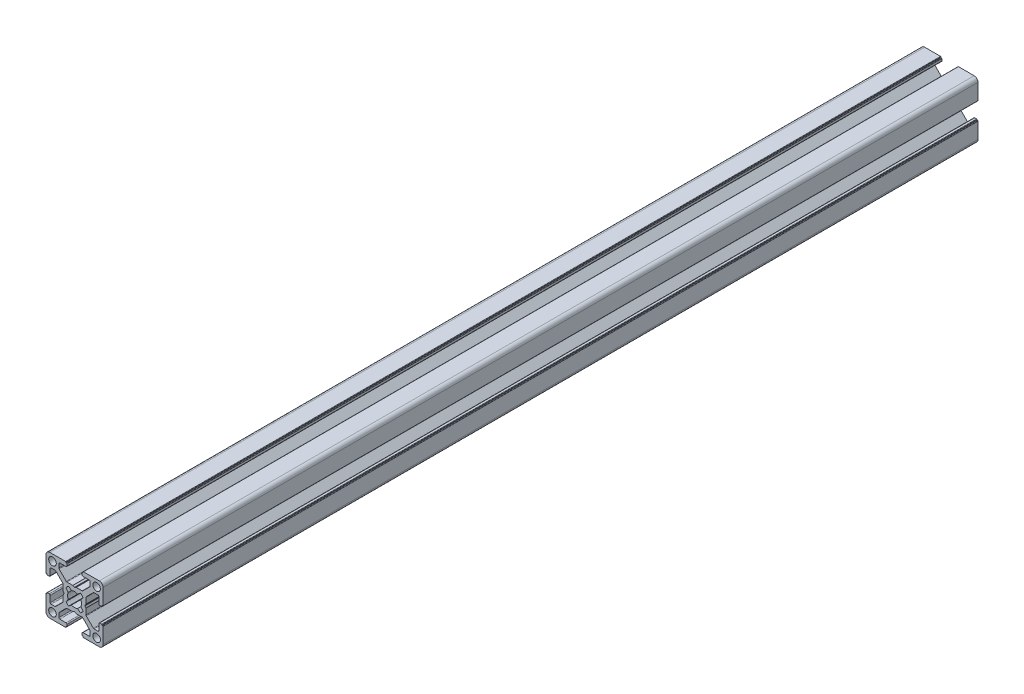
SolidWorks part; units mm, degrees
ref_plane "Alzado" through (0, 0, 0) normal (0, 0, 1) x (1, 0, 0)
ref_plane "Planta" through (0, 0, 0) normal (0, 1, 0) x (1, 0, 0)
ref_plane "Vista lateral" through (0, 0, 0) normal (1, 0, 0) x (0, 0, -1)
ref_plane "Plano1" through (0, 0, 1000) normal (0, 0, 1) x (1, 0, 0)
sketch "Croquis1" plane through (0, 0, 1000) normal (0, 0, 1) x (1, 0, 0)
  line L16 (-7.8359, -10.4816) -> (-6.3001, -11.7194)
  line L17 (-3.0999, -11.7194) -> (-1.5641, -10.4816)
  line L18 (-0.1947, -11.8453) -> (-1.4194, -13.3999)
  line L19 (-1.4194, -16.6001) -> (-0.1947, -18.1547)
  line L20 (-1.5641, -19.5184) -> (-3.0999, -18.2806)
  line L21 (-6.3001, -18.2806) -> (-7.8359, -19.5184)
  line L22 (-9.2053, -18.1547) -> (-7.9806, -16.6001)
  line L23 (-7.9806, -13.3999) -> (-9.2053, -11.8453)
  line L24 (9.8, -10.5) -> (10.1, -10.5)
  line L25 (10.3, -10.3) -> (10.3, -2)
  line L26 (8.3, 0) -> (0, 0)
  line L27 (-0.2, -0.2) -> (-0.2, -0.5)
  line L28 (-0.2, -0.5) -> (-0.5, -0.5)
  line L29 (-0.7, -0.7) -> (-0.7, -1.7)
  line L30 (-0.2, -2.2) -> (3.05, -2.2)
  line L31 (3.55, -2.7) -> (3.55, -4.7431)
  line L32 (3.4037, -5.0964) -> (-0.3491, -8.8534)
  line L33 (-0.7028, -9) -> (-3.7468, -9)
  line L34 (-3.8462, -9.0264) -> (-4.6006, -9.4583)
  line L35 (-4.7994, -9.4583) -> (-5.5538, -9.0264)
  line L36 (-5.6532, -9) -> (-8.6972, -9)
  line L37 (-9.0509, -8.8534) -> (-12.8037, -5.0964)
  line L38 (-12.95, -4.7431) -> (-12.95, -2.7)
  line L39 (-12.45, -2.2) -> (-9.2, -2.2)
  line L40 (-8.7, -1.7) -> (-8.7, -0.7)
  line L41 (-8.9, -0.5) -> (-9.2, -0.5)
  line L42 (-9.2, -0.5) -> (-9.2, -0.2)
  line L43 (-9.4, 0) -> (-17.7, 0)
  line L44 (-19.7, -2) -> (-19.7, -10.3)
  line L45 (-19.5, -10.5) -> (-19.2, -10.5)
  line L46 (-19.2, -10.5) -> (-19.2, -10.8)
  line L47 (-19, -11) -> (-18, -11)
  line L48 (-17.5, -10.5) -> (-17.5, -7.25)
  line L49 (-17, -6.75) -> (-14.9569, -6.75)
  line L50 (-14.6036, -6.8963) -> (-10.8466, -10.6491)
  line L51 (-10.7, -11.0028) -> (-10.7, -14.0468)
  line L52 (-10.6736, -14.1462) -> (-10.2417, -14.9006)
  line L53 (-10.2417, -15.0994) -> (-10.6736, -15.8538)
  line L54 (-10.7, -15.9532) -> (-10.7, -18.9972)
  line L55 (-10.8466, -19.3509) -> (-14.6036, -23.1037)
  line L56 (-14.9569, -23.25) -> (-17, -23.25)
  line L57 (-17.5, -22.75) -> (-17.5, -19.5)
  line L58 (-18, -19) -> (-19, -19)
  line L59 (-19.2, -19.2) -> (-19.2, -19.5)
  line L60 (-19.2, -19.5) -> (-19.5, -19.5)
  line L61 (-19.7, -19.7) -> (-19.7, -28)
  line L62 (-17.7, -30) -> (-9.4, -30)
  line L63 (-9.2, -29.8) -> (-9.2, -29.5)
  line L64 (-9.2, -29.5) -> (-8.9, -29.5)
  line L65 (-8.7, -29.3) -> (-8.7, -28.3)
  line L66 (-9.2, -27.8) -> (-12.45, -27.8)
  line L67 (-12.95, -27.3) -> (-12.95, -25.2569)
  line L68 (-12.8037, -24.9036) -> (-9.0509, -21.1466)
  line L69 (-8.6972, -21) -> (-5.6532, -21)
  line L70 (-5.5538, -20.9736) -> (-4.7994, -20.5417)
  line L71 (-4.6006, -20.5417) -> (-3.8462, -20.9736)
  line L72 (-3.7468, -21) -> (-0.7028, -21)
  line L73 (-0.3491, -21.1466) -> (3.4037, -24.9036)
  line L74 (3.55, -25.2569) -> (3.55, -27.3)
  line L75 (3.05, -27.8) -> (-0.2, -27.8)
  line L76 (-0.7, -28.3) -> (-0.7, -29.3)
  line L77 (-0.5, -29.5) -> (-0.2, -29.5)
  line L78 (-0.2, -29.5) -> (-0.2, -29.8)
  line L79 (0, -30) -> (8.3, -30)
  line L80 (10.3, -28) -> (10.3, -19.7)
  line L81 (10.1, -19.5) -> (9.8, -19.5)
  line L82 (9.8, -19.5) -> (9.8, -19.2)
  line L83 (9.6, -19) -> (8.6, -19)
  line L84 (8.1, -19.5) -> (8.1, -22.75)
  line L85 (7.6, -23.25) -> (5.5569, -23.25)
  line L86 (5.2036, -23.1037) -> (1.4466, -19.3509)
  line L87 (1.3, -18.9972) -> (1.3, -15.9532)
  line L88 (1.2736, -15.8538) -> (0.8417, -15.0994)
  line L89 (0.8417, -14.9006) -> (1.2736, -14.1462)
  line L90 (1.3, -14.0468) -> (1.3, -11.0028)
  line L91 (1.4466, -10.6491) -> (5.2036, -6.8963)
  line L92 (5.5569, -6.75) -> (7.6, -6.75)
  line L93 (8.1, -7.25) -> (8.1, -10.5)
  line L94 (8.6, -11) -> (9.6, -11)
  line L95 (9.8, -10.8) -> (9.8, -10.5)
  line L96 (8, -2.3) -> (5.8, -4.5) construction
  line L97 (-15.2, -2.3) -> (-17.4, -4.5) construction
  line L98 (-4.7, -15) -> (6.9, -15) construction
  arc A16 (-9.2053, -11.8453) -> (-7.8359, -10.4816) centre (-4.7, -15) cw
  arc A17 (-6.3001, -11.7194) -> (-3.0999, -11.7194) centre (-4.7, -15) cw
  arc A18 (-1.5641, -10.4816) -> (-0.1947, -11.8453) centre (-4.7, -15) cw
  arc A19 (-1.4194, -13.3999) -> (-1.4194, -16.6001) centre (-4.7, -15) cw
  arc A20 (-0.1947, -18.1547) -> (-1.5641, -19.5184) centre (-4.7, -15) cw
  arc A21 (-3.0999, -18.2806) -> (-6.3001, -18.2806) centre (-4.7, -15) cw
  arc A22 (-7.8359, -19.5184) -> (-9.2053, -18.1547) centre (-4.7, -15) cw
  arc A23 (-7.9806, -16.6001) -> (-7.9806, -13.3999) centre (-4.7, -15) cw
  arc A24 (10.1, -10.5) -> (10.3, -10.3) centre (10.1, -10.3) ccw
  arc A25 (10.3, -2) -> (8.3, 0) centre (8.3, -2) ccw
  arc A26 (0, 0) -> (-0.2, -0.2) centre (0, -0.2) ccw
  arc A27 (-0.5, -0.5) -> (-0.7, -0.7) centre (-0.5, -0.7) ccw
  arc A28 (-0.7, -1.7) -> (-0.2, -2.2) centre (-0.2, -1.7) ccw
  arc A29 (3.05, -2.2) -> (3.55, -2.7) centre (3.05, -2.7) cw
  arc A30 (3.55, -4.7431) -> (3.4037, -5.0964) centre (3.05, -4.7431) cw
  arc A31 (-0.3491, -8.8534) -> (-0.7028, -9) centre (-0.7028, -8.5) cw
  arc A32 (-3.7468, -9) -> (-3.8462, -9.0264) centre (-3.7468, -9.2) ccw
  arc A33 (-4.6006, -9.4583) -> (-4.7994, -9.4583) centre (-4.7, -9.2847) cw
  arc A34 (-5.5538, -9.0264) -> (-5.6532, -9) centre (-5.6532, -9.2) ccw
  arc A35 (-8.6972, -9) -> (-9.0509, -8.8534) centre (-8.6972, -8.5) cw
  arc A36 (-12.8037, -5.0964) -> (-12.95, -4.7431) centre (-12.45, -4.7431) cw
  arc A37 (-12.95, -2.7) -> (-12.45, -2.2) centre (-12.45, -2.7) cw
  arc A38 (-9.2, -2.2) -> (-8.7, -1.7) centre (-9.2, -1.7) ccw
  arc A39 (-8.7, -0.7) -> (-8.9, -0.5) centre (-8.9, -0.7) ccw
  arc A40 (-9.2, -0.2) -> (-9.4, 0) centre (-9.4, -0.2) ccw
  arc A41 (-17.7, 0) -> (-19.7, -2) centre (-17.7, -2) ccw
  arc A42 (-19.7, -10.3) -> (-19.5, -10.5) centre (-19.5, -10.3) ccw
  arc A43 (-19.2, -10.8) -> (-19, -11) centre (-19, -10.8) ccw
  arc A44 (-18, -11) -> (-17.5, -10.5) centre (-18, -10.5) ccw
  arc A45 (-17.5, -7.25) -> (-17, -6.75) centre (-17, -7.25) cw
  arc A46 (-14.9569, -6.75) -> (-14.6036, -6.8963) centre (-14.9569, -7.25) cw
  arc A47 (-10.8466, -10.6491) -> (-10.7, -11.0028) centre (-11.2, -11.0028) cw
  arc A48 (-10.7, -14.0468) -> (-10.6736, -14.1462) centre (-10.5, -14.0468) ccw
  arc A49 (-10.2417, -14.9006) -> (-10.2417, -15.0994) centre (-10.4153, -15) cw
  arc A50 (-10.6736, -15.8538) -> (-10.7, -15.9532) centre (-10.5, -15.9532) ccw
  arc A51 (-10.7, -18.9972) -> (-10.8466, -19.3509) centre (-11.2, -18.9972) cw
  arc A52 (-14.6036, -23.1037) -> (-14.9569, -23.25) centre (-14.9569, -22.75) cw
  arc A53 (-17, -23.25) -> (-17.5, -22.75) centre (-17, -22.75) cw
  arc A54 (-17.5, -19.5) -> (-18, -19) centre (-18, -19.5) ccw
  arc A55 (-19, -19) -> (-19.2, -19.2) centre (-19, -19.2) ccw
  arc A56 (-19.5, -19.5) -> (-19.7, -19.7) centre (-19.5, -19.7) ccw
  arc A57 (-19.7, -28) -> (-17.7, -30) centre (-17.7, -28) ccw
  arc A58 (-9.4, -30) -> (-9.2, -29.8) centre (-9.4, -29.8) ccw
  arc A59 (-8.9, -29.5) -> (-8.7, -29.3) centre (-8.9, -29.3) ccw
  arc A60 (-8.7, -28.3) -> (-9.2, -27.8) centre (-9.2, -28.3) ccw
  arc A61 (-12.45, -27.8) -> (-12.95, -27.3) centre (-12.45, -27.3) cw
  arc A62 (-12.95, -25.2569) -> (-12.8037, -24.9036) centre (-12.45, -25.2569) cw
  arc A63 (-9.0509, -21.1466) -> (-8.6972, -21) centre (-8.6972, -21.5) cw
  arc A64 (-5.6532, -21) -> (-5.5538, -20.9736) centre (-5.6532, -20.8) ccw
  arc A65 (-4.7994, -20.5417) -> (-4.6006, -20.5417) centre (-4.7, -20.7153) cw
  arc A66 (-3.8462, -20.9736) -> (-3.7468, -21) centre (-3.7468, -20.8) ccw
  arc A67 (-0.7028, -21) -> (-0.3491, -21.1466) centre (-0.7028, -21.5) cw
  arc A68 (3.4037, -24.9036) -> (3.55, -25.2569) centre (3.05, -25.2569) cw
  arc A69 (3.55, -27.3) -> (3.05, -27.8) centre (3.05, -27.3) cw
  arc A70 (-0.2, -27.8) -> (-0.7, -28.3) centre (-0.2, -28.3) ccw
  arc A71 (-0.7, -29.3) -> (-0.5, -29.5) centre (-0.5, -29.3) ccw
  arc A72 (-0.2, -29.8) -> (0, -30) centre (0, -29.8) ccw
  arc A73 (8.3, -30) -> (10.3, -28) centre (8.3, -28) ccw
  arc A74 (10.3, -19.7) -> (10.1, -19.5) centre (10.1, -19.7) ccw
  arc A75 (9.8, -19.2) -> (9.6, -19) centre (9.6, -19.2) ccw
  arc A76 (8.6, -19) -> (8.1, -19.5) centre (8.6, -19.5) ccw
  arc A77 (8.1, -22.75) -> (7.6, -23.25) centre (7.6, -22.75) cw
  arc A78 (5.5569, -23.25) -> (5.2036, -23.1037) centre (5.5569, -22.75) cw
  arc A79 (1.4466, -19.3509) -> (1.3, -18.9972) centre (1.8, -18.9972) cw
  arc A80 (1.3, -15.9532) -> (1.2736, -15.8538) centre (1.1, -15.9532) ccw
  arc A81 (0.8417, -15.0994) -> (0.8417, -14.9006) centre (1.0153, -15) cw
  arc A82 (1.2736, -14.1462) -> (1.3, -14.0468) centre (1.1, -14.0468) ccw
  arc A83 (1.3, -11.0028) -> (1.4466, -10.6491) centre (1.8, -11.0028) cw
  arc A84 (5.2036, -6.8963) -> (5.5569, -6.75) centre (5.5569, -7.25) cw
  arc A85 (7.6, -6.75) -> (8.1, -7.25) centre (7.6, -7.25) cw
  arc A86 (8.1, -10.5) -> (8.6, -11) centre (8.6, -10.5) ccw
  arc A87 (9.6, -11) -> (9.8, -10.8) centre (9.6, -10.8) ccw
  circle A88 centre (-16.3, -3.4) radius 2
  circle A89 centre (6.9, -3.4) radius 2
  circle A90 centre (-16.3, -26.6) radius 2
  circle A91 centre (6.9, -26.6) radius 2
  dimension "D3" = 4
  dimension "D1" = 30
  dimension "D2" = 30
  dimension "D4" = 23.2
  dimension "D5" = 23.2
extrude "Saliente-Extruir1" add sketch "Croquis1" against normal blind 460
